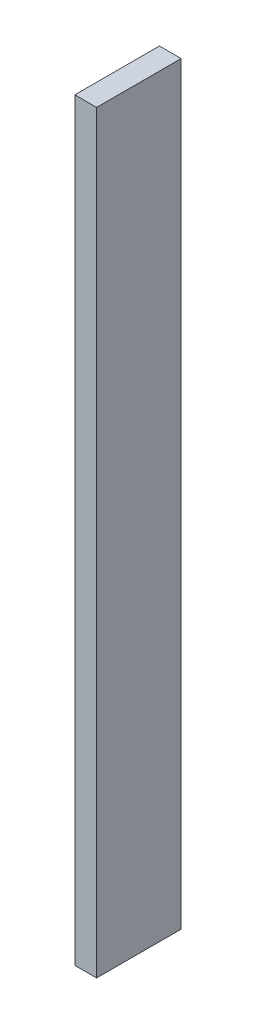
SolidWorks part; units mm, degrees
ref_plane "Plan de face" through (0, 0, 0) normal (0, 0, 1) x (1, 0, 0)
ref_plane "Plan de dessus" through (0, 0, 0) normal (0, 1, 0) x (1, 0, 0)
ref_plane "Plan de droite" through (0, 0, 0) normal (1, 0, 0) x (0, 0, -1)
sketch "Esquisse1" plane through (0, 0, 0) normal (0, 0, 1) x (1, 0, 0)
  line L0 (-60, 181) -> (60, 181) construction
  line L1 (-57.85, 156) -> (-66.85, 156)
  line L2 (-57.85, 156) -> (-57.85, -156)
  line L3 (-57.85, -156) -> (-66.85, -156)
  line L4 (-66.85, 156) -> (-66.85, -156)
  line L5 (60, -181) -> (-60, -181) construction
  line L6 (-56.85, -126.7) -> (-56.85, 156.3) construction
  line L7 (-67.85, 156.3) -> (-67.85, -126.7) construction
  point P6 (-62.35, -156)
  dimension "D1" = 25
  dimension "D2" = 25
  dimension "D3" = 1
  dimension "D4" = 1
extrude "Boss.-Extru.1" add sketch "Esquisse1" along normal blind 35 contours L2 L3 L4 L1
